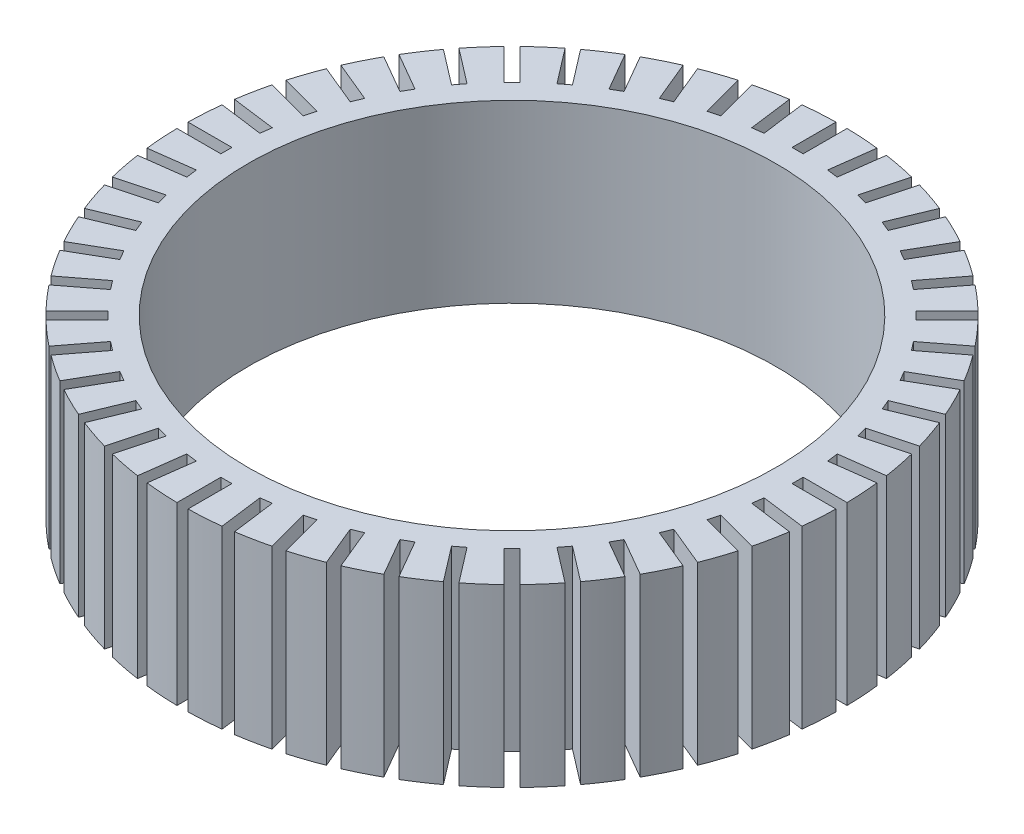
SolidWorks part; units mm, degrees
ref_plane "Front Plane" through (0, 0, 0) normal (0, 0, 1) x (1, 0, 0)
ref_plane "Top Plane" through (0, 0, 0) normal (0, 1, 0) x (1, 0, 0)
ref_plane "Right Plane" through (0, 0, 0) normal (1, 0, 0) x (0, 0, -1)
ref_axis "Axis1" through (0, 80.4, 0) along (0, -1, 0)
sketch "Sketch2" plane through (0, 0, 0) normal (0, 0, 1) x (1, 0, 0)
  line L0 (-23.8125, 0) -> (-23.8125, 12.7)
  line L1 (-23.8125, 12.7) -> (-19.05, 12.7)
  line L2 (-19.05, 12.7) -> (-19.05, 0)
  line L3 (-19.05, 0) -> (-23.8125, 0)
  dimension "D1" = 19.05
  dimension "D2" = 12.7
  dimension "D3" = 4.7625
revolve "Revolve1" add sketch "Sketch2" angle 360 about axis through (0, 80.4, 0) along (0, -1, 0)
sketch "Sketch3" plane through (0, 0, 0) normal (0, 1, 0) x (1, 0, 0)
  line L0 (-19.05, 0) -> (-23.8125, 0) construction
  line L1 (-46.0375, 0.4001) -> (-20.6375, 0.4001)
  line L2 (-46.0375, 0.4001) -> (-46.0375, -0.4001)
  line L3 (-46.0375, -0.4001) -> (-20.6375, -0.4001)
  line L4 (-20.6375, 0.4001) -> (-20.6375, -0.4001)
  point P4 (-20.6375, 0)
  dimension "D1" = 1.5875
  dimension "D2" = 0.8001
  dimension "D3" = 25.4
extrude "Cut-Extrude1" cut sketch "Sketch3" along normal up to surface (12.7 mm away) up to face at (0, 12.7, 23.8125)
pattern_circular "CirPattern1" count 48 over 360 about axis through (0, 0, 0) along (0, 1, 0) of "Cut-Extrude1"
